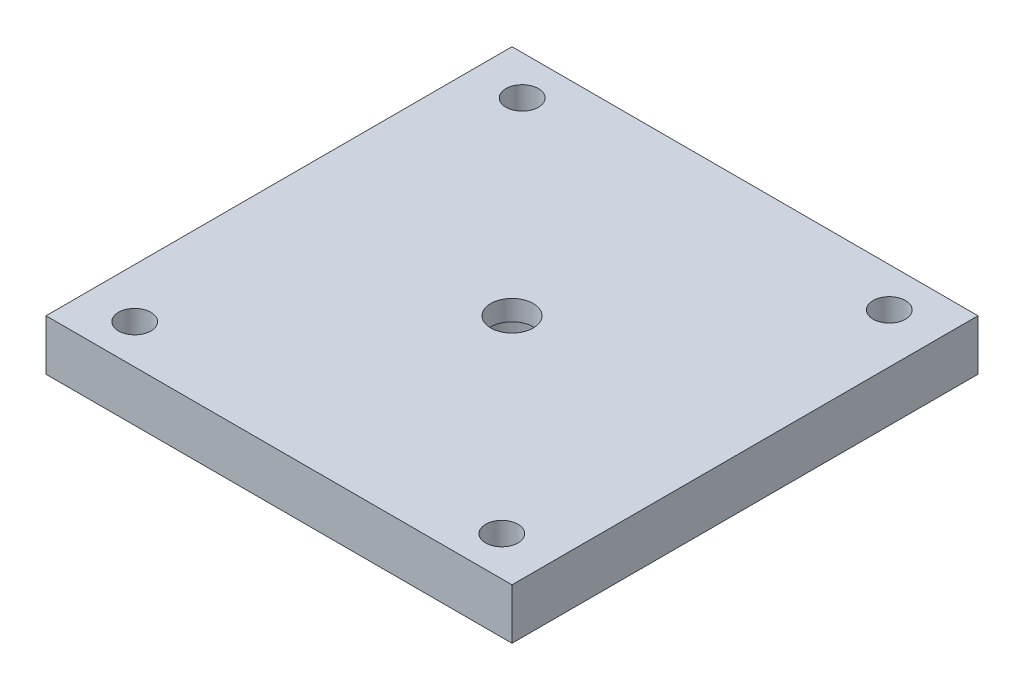
SolidWorks part; units mm, degrees
ref_plane "Front Plane" through (0, 0, 0) normal (0, 0, 1) x (1, 0, 0)
ref_plane "Top Plane" through (0, 0, 0) normal (0, 1, 0) x (1, 0, 0)
ref_plane "Right Plane" through (0, 0, 0) normal (1, 0, 0) x (0, 0, -1)
sketch "Sketch2" plane through (0, 0, 0) normal (0, 1, 0) x (1, 0, 0)
  line L1 (-23, -23) -> (23, -23)
  line L2 (-23, -23) -> (-23, 23)
  line L3 (-23, 23) -> (23, 23)
  line L4 (23, -23) -> (23, 23)
  line L5 (-23, -23) -> (23, 23) construction
  line L6 (-23, 23) -> (23, -23) construction
  point P0 (0, 0)
extrude "Boss-Extrude1" add sketch "Sketch2" along normal blind 5
sketch "Sketch4" plane through (0, 0, 0) normal (0, 1, 0) x (1, 0, 0)
  circle A0 centre (0, 0) radius 4.1
extrude "Cut-Extrude2" cut sketch "Sketch4" along normal blind 3
sketch "Sketch5" plane through (0, 0, 0) normal (0, 1, 0) x (1, 0, 0)
  circle A0 centre (0, 0) radius 2.1
extrude "Cut-Extrude4" cut sketch "Sketch5" along normal through all
sketch "Sketch6" plane through (0, 0, 0) normal (0, 1, 0) x (1, 0, 0)
  line L0 (18.12, 19.125) -> (-18.12, 19.125) construction
  line L2 (-18.12, 19.125) -> (-18.12, -19.125) construction
  line L3 (-18.12, -19.125) -> (18.12, -19.125) construction
  line L10 (0, 0) -> (18.12, 0) construction
  line L11 (18.12, 0) -> (18.12, 19.125) construction
  circle A4 centre (18.12, 19.125) radius 1.6
  circle A5 centre (-18.12, 19.125) radius 1.6
  circle A6 centre (-18.12, -19.125) radius 1.6
  circle A7 centre (18.12, -19.125) radius 1.6
extrude "Cut-Extrude5" cut sketch "Sketch6" along normal blind 5
